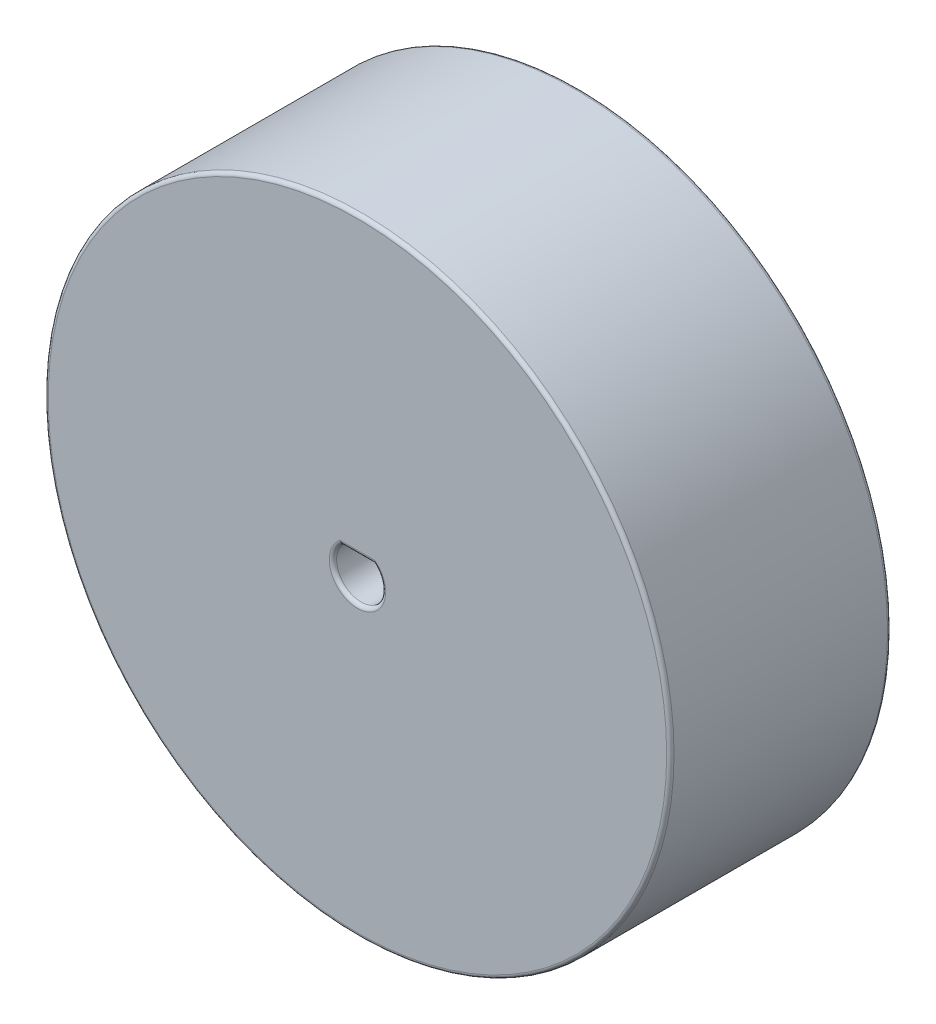
SolidWorks part; units mm, degrees
material "PET"
ref_plane "Plan de face" through (0, 0, 0) normal (0, 0, 1) x (1, 0, 0)
ref_plane "Plan de dessus" through (0, 0, 0) normal (0, 1, 0) x (1, 0, 0)
ref_plane "Plan de droite" through (0, 0, 0) normal (1, 0, 0) x (0, 0, -1)
sketch "Esquisse1" plane through (0, 0, 0) normal (0, 0, 1) x (1, 0, 0)
  circle A0 centre (0, 0) radius 25.5
  dimension "D1" = 51
extrude "Boss.-Extru.1" add sketch "Esquisse1" along normal blind 18
sketch "Esquisse2" plane through (0, 0, 18) normal (0, 0, 1) x (1, 0, 0)
  line L0 (0, 0) -> (0, 1.5) construction
  line L1 (1.3229, 1.5) -> (-1.3229, 1.5)
  arc A0 (1.3229, 1.5) -> (-1.3229, 1.5) centre (0, 0) cw
  dimension "D1" = 1.5
  dimension "D2" = 2
extrude "Enlèv. mat.-Extru.2" cut sketch "Esquisse2" against normal blind 10
sketch "Esquisse3" plane through (0, 0, 0) normal (0, 0, -1) x (-1, 0, 0)
  line L2 (1.5, -1.5) -> (1.5, -25.4558)
  line L3 (-1.5, -1.5) -> (-1.5, -25.4558)
  line L4 (-1.5, -1.5) -> (-25.4558, -1.5)
  line L5 (-1.5, 1.5) -> (-25.4558, 1.5)
  line L6 (-1.5, 1.5) -> (-1.5, 25.4558)
  line L7 (1.5, 1.5) -> (1.5, 25.4558)
  line L8 (1.5, 1.5) -> (25.4558, 1.5)
  line L9 (1.5, -1.5) -> (25.4558, -1.5)
  circle A0 centre (0, 0) radius 25.5 construction
  circle A1 centre (0, 0) radius 25.5
  circle A2 centre (0, 0) radius 24
  circle A3 centre (0, 0) radius 4.0002
  point P0 (-1.5, 1.5)
  point P1 (-1.5, -1.5)
  point P2 (1.5, 1.5)
  point P3 (1.5, -1.5)
  dimension "D1" = 48
extrude "Enlèv. mat.-Extru.4" cut sketch "Esquisse3" against normal blind 5 contours A3 L8 A2 L7 | A3 L6 A2 L5 | A3 L4 A2 L3 | A3 L2 A2 L9
fillet "Congé1" radius 0.3 4 edges at (0, 1.5, 18) (0, -2, 18) (25.5, 0, 18) (25.5, 0, 0)
